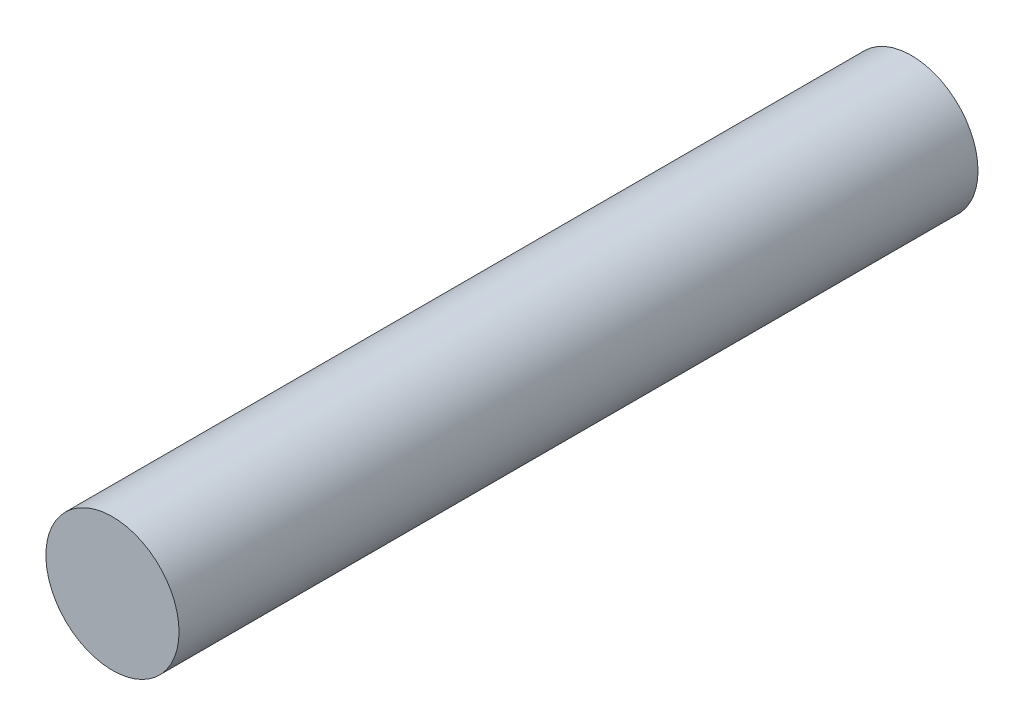
SolidWorks part; units mm, degrees
ref_plane "Front Plane" through (0, 0, 0) normal (0, 0, 1) x (1, 0, 0)
ref_plane "Top Plane" through (0, 0, 0) normal (0, 1, 0) x (1, 0, 0)
ref_plane "Right Plane" through (0, 0, 0) normal (1, 0, 0) x (0, 0, -1)
sketch "Sketch1" plane through (0, 0, 0) normal (0, 0, 1) x (1, 0, 0)
  circle A0 centre (0, 0) radius 1.5875
extrude "Boss-Extrude1" add sketch "Sketch1" along normal blind 19.05
